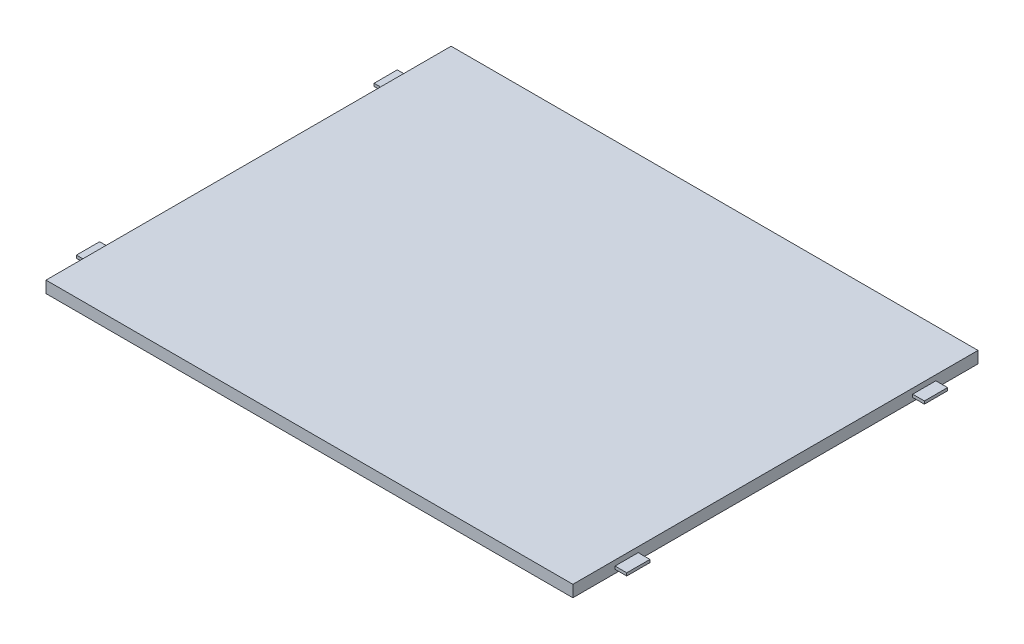
SolidWorks part; units mm, degrees
ref_plane "Front Plane" through (0, 0, 0) normal (0, 0, 1) x (1, 0, 0)
ref_plane "Top Plane" through (0, 0, 0) normal (0, 1, 0) x (1, 0, 0)
ref_plane "Right Plane" through (0, 0, 0) normal (1, 0, 0) x (0, 0, -1)
sketch "Sketch1" plane through (0, 0, 0) normal (0, 1, 0) x (1, 0, 0)
  line L1 (0, 0) -> (225, 0)
  line L2 (0, 0) -> (0, 173)
  line L3 (0, 173) -> (225, 173)
  line L4 (225, 0) -> (225, 173)
  dimension "D1" = 225
  dimension "D2" = 173
extrude "Boss-Extrude1" add sketch "Sketch1" along normal blind 5
sketch "Sketch2" plane through (0, 0, 0) normal (-1, 0, 0) x (0, 0, 1)
  line L0 (0, 5) -> (0, 0) construction
  line L1 (-145.1, 2.75) -> (-155, 2.75)
  line L2 (-145.1, 2.75) -> (-145.1, 1.55)
  line L3 (-145.1, 1.55) -> (-155, 1.55)
  line L4 (-155, 2.75) -> (-155, 1.55)
  line L5 (-27.9, 2.75) -> (-18, 2.75)
  line L6 (-27.9, 2.75) -> (-27.9, 1.55)
  line L7 (-27.9, 1.55) -> (-18, 1.55)
  line L8 (-18, 2.75) -> (-18, 1.55)
  line L9 (-173, 5) -> (0, 5) construction
  line L10 (-86.5, 5) -> (-86.5, 11.7158) construction
  dimension "D1" = 18
  dimension "D2" = 1.2
  dimension "D3" = 2.25
  dimension "D4" = 9.9
extrude "Boss-Extrude2" add sketch "Sketch2" along normal blind 5
sketch "Sketch3" plane through (225, 0, 0) normal (1, 0, 0) x (0, 0, -1)
  line L5 (27.9, 2.75) -> (18, 2.75)
  line L6 (18, 2.75) -> (18, 1.55)
  line L7 (18, 1.55) -> (27.9, 1.55)
  line L8 (27.9, 1.55) -> (27.9, 2.75)
  line L9 (27.9, 2.75) -> (18, 2.75)
  line L10 (18, 2.75) -> (18, 1.55)
  line L11 (18, 1.55) -> (27.9, 1.55)
  line L12 (27.9, 1.55) -> (27.9, 2.75)
  line L13 (155, 2.75) -> (145.1, 2.75)
  line L14 (155, 1.55) -> (155, 2.75)
  line L15 (145.1, 1.55) -> (155, 1.55)
  line L16 (145.1, 2.75) -> (145.1, 1.55)
  line L17 (155, 2.75) -> (145.1, 2.75)
  line L18 (155, 1.55) -> (155, 2.75)
  line L19 (145.1, 1.55) -> (155, 1.55)
  line L20 (145.1, 2.75) -> (145.1, 1.55)
  dimension "D1" = 0
  dimension "D2" = 0
extrude "Boss-Extrude3" add sketch "Sketch3" along normal blind 5
